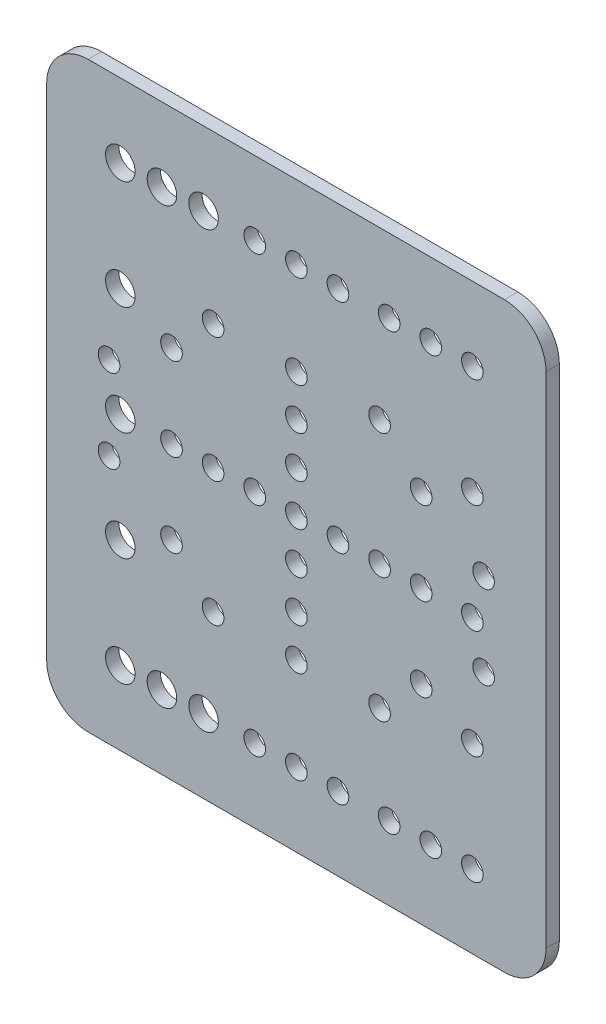
SolidWorks part; units mm, degrees
ref_plane "Front Plane" through (0, 0, 0) normal (0, 0, 1) x (1, 0, 0)
ref_plane "Top Plane" through (0, 0, 0) normal (0, 1, 0) x (1, 0, 0)
ref_plane "Right Plane" through (0, 0, 0) normal (1, 0, 0) x (0, 0, -1)
sketch "Sketch1" plane through (0, 0, 0) normal (0, 0, 1) x (1, 0, 0)
  line L0 (-60, 0) -> (60, 0) construction
  line L1 (-60, 70) -> (60, 70)
  line L2 (-60, 70) -> (-60, -70)
  line L3 (-60, -70) -> (60, -70)
  line L4 (60, 70) -> (60, -70)
  circle A0 centre (0, 0) radius 2.6
  circle A1 centre (10, 0) radius 2.6
  circle A2 centre (20, 0) radius 2.6
  circle A3 centre (30, 0) radius 2.6
  circle A4 centre (-10, 0) radius 2.6
  circle A5 centre (-20, 0) radius 2.6
  circle A6 centre (-30, 0) radius 2.6
  circle A7 centre (0, 10) radius 2.6
  circle A8 centre (0, 20) radius 2.6
  circle A9 centre (0, 30) radius 2.6
  circle A10 centre (0, -10) radius 2.6
  circle A11 centre (0, -20) radius 2.6
  circle A12 centre (0, -30) radius 2.6
  circle A13 centre (42.3, 0) radius 2.6
  circle A14 centre (-42.3, 0) radius 3.55
  circle A15 centre (-42.3, 26.15) radius 3.55
  circle A16 centre (-42.3, 52.3) radius 3.55
  circle A17 centre (-42.3, -26.15) radius 3.55
  circle A18 centre (-42.3, -52.3) radius 3.55
  circle A19 centre (42.3, 26.15) radius 2.6
  circle A20 centre (42.3, 52.3) radius 2.6
  circle A21 centre (42.3, -26.15) radius 2.6
  circle A22 centre (42.3, -52.3) radius 2.6
  circle A23 centre (-32.3, 52.3) radius 3.55
  circle A24 centre (-22.3, 52.3) radius 3.55
  circle A25 centre (-32.3, -52.3) radius 3.55
  circle A26 centre (-22.3, -52.3) radius 3.55
  circle A27 centre (32.3, 52.3) radius 2.6
  circle A28 centre (22.3, 52.3) radius 2.6
  circle A29 centre (32.3, -52.3) radius 2.6
  circle A30 centre (22.3, -52.3) radius 2.6
  circle A31 centre (0, 52.3) radius 2.6
  circle A32 centre (10, 52.3) radius 2.6
  circle A33 centre (-10, 52.3) radius 2.6
  circle A34 centre (-20, 30) radius 2.6
  circle A35 centre (20, 30) radius 2.6
  circle A36 centre (-30, 20) radius 2.6
  circle A37 centre (30, 20) radius 2.6
  circle A38 centre (-45, 10) radius 2.6
  circle A39 centre (45, 10) radius 2.6
  circle A40 centre (45, -10) radius 2.6
  circle A41 centre (30, -20) radius 2.6
  circle A42 centre (20, -30) radius 2.6
  circle A43 centre (10, -52.3) radius 2.6
  circle A44 centre (0, -52.3) radius 2.6
  circle A45 centre (-10, -52.3) radius 2.6
  circle A46 centre (-20, -30) radius 2.6
  circle A47 centre (-30, -20) radius 2.6
  circle A48 centre (-45, -10) radius 2.6
  point P0 (0, 0)
  point P6 (-60, 0)
  point P7 (60, 0)
  point P8 (0, 70)
  dimension "D3" = 5.2
  dimension "D9" = 7.1
  dimension "D1" = 140
  dimension "D2" = 120
  dimension "D7" = 42.3
  dimension "D8" = 42.3
  dimension "D12" = 3
  dimension "D15" = 17.7
  dimension "D16" = 17.7
  dimension "D17" = 17.7
  dimension "D18" = 17.7
  dimension "D19" = 10
  dimension "D20" = 10
  dimension "D21" = 10
  dimension "D22" = 10
  dimension "D23" = 10
  dimension "D24" = 10
  dimension "D25" = 10
  dimension "D26" = 10
  dimension "D27" = 45
  dimension "D28" = 45
  dimension "D10" = 4
  dimension "D4" = 4
  dimension "D5" = 4
  dimension "D6" = 4
  dimension "D11" = 3
  dimension "D13" = 3
  dimension "D14" = 3
extrude "Boss-Extrude1" add sketch "Sketch1" against normal blind 3.2
sketch "Sketch2" plane through (0, 0, 0) normal (0, 0, 1) x (1, 0, 0)
  circle A0 centre (0, 0) radius 2.6 construction
  circle A1 centre (0, 0) radius 2.6
fillet "Fillet1" radius 10 4 edges at (-60, -70, -1.6) (60, -70, -1.6) (60, 70, -1.6) (-60, 70, -1.6)
